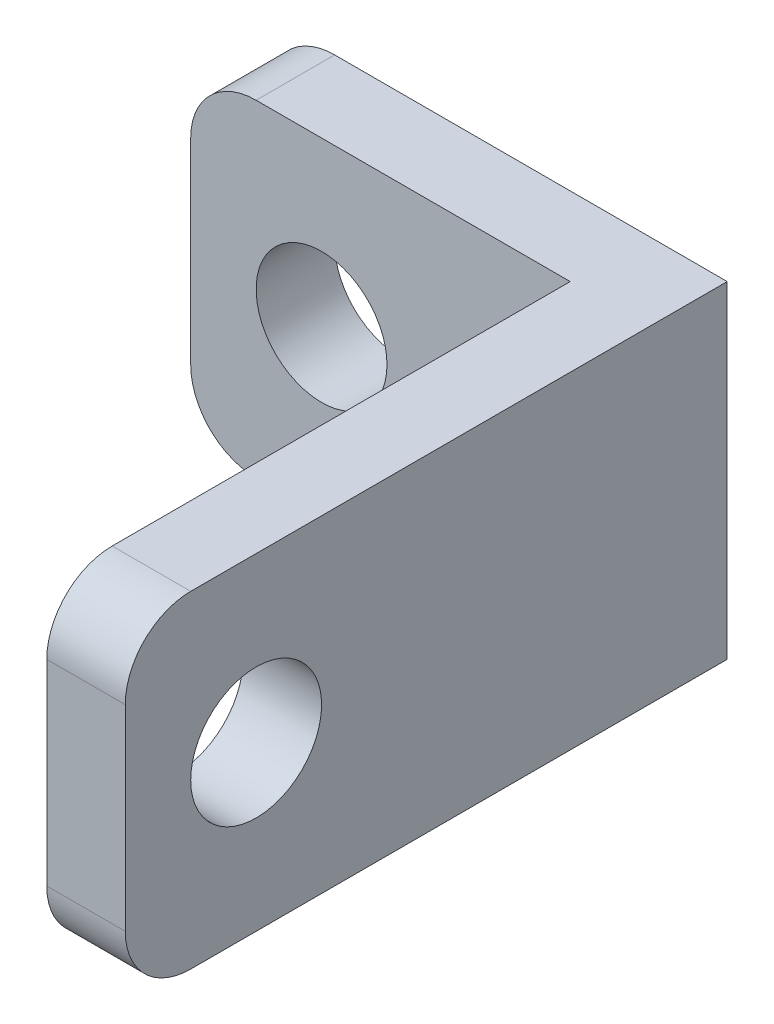
SolidWorks part; units mm, degrees
ref_plane "Front" through (0, 0, 0) normal (0, 0, 1) x (1, 0, 0)
ref_plane "Top" through (0, 0, 0) normal (0, 1, 0) x (1, 0, 0)
ref_plane "Right" through (0, 0, 0) normal (1, 0, 0) x (0, 0, -1)
sketch "草图1" plane through (0, 0, 0) normal (0, 0, 1) x (1, 0, 0)
  line L3 (1, 0) -> (7, 0)
  line L4 (0, 1) -> (0, 4)
  line L5 (1, 5) -> (7, 5)
  line L6 (7, 0) -> (7, 5)
  circle A2 centre (2, 2.5) radius 1
  arc A3 (0, 4) -> (1, 5) centre (1, 4) cw
  arc A4 (1, 0) -> (0, 1) centre (1, 1) cw
  point P13 (0, 0)
  dimension "D1" = 1
  dimension "D2" = 1
  dimension "D3" = 2
  dimension "D5" = 2.5
  dimension "D4" = 2.5
extrude "凸台-拉伸1" add sketch "草图1" along normal blind 1.2
sketch "草图2" plane through (0, 0, 1.2) normal (0, 0, -1) x (-1, 0, 0)
  line L0 (-7, 0) -> (-7, 5) construction
  line L1 (-5.8, 0) -> (-7, 0)
  line L2 (-5.8, 0) -> (-5.8, 5)
  line L3 (-5.8, 5) -> (-7, 5)
  line L4 (-7, 0) -> (-7, 5)
  line L5 (-7, 5) -> (-1, 5) construction
  dimension "D1" = 0
  dimension "D2" = 1.2
  dimension "D3" = 0
extrude "凸台-拉伸2" add sketch "草图2" against normal blind 8
fillet "圆角1" radius 1 2 edges at (6.4, 0, 9.2) (6.4, 5, 9.2)
sketch "草图4" plane through (5.8, 0, 0) normal (-1, 0, 0) x (0, 0, 1)
  line L2 (9.2, 1) -> (9.2, 4) construction
  circle A0 centre (7.2, 2.5) radius 1
  dimension "D1" = 2
extrude "切除-拉伸1" cut sketch "草图4" against normal blind 2
